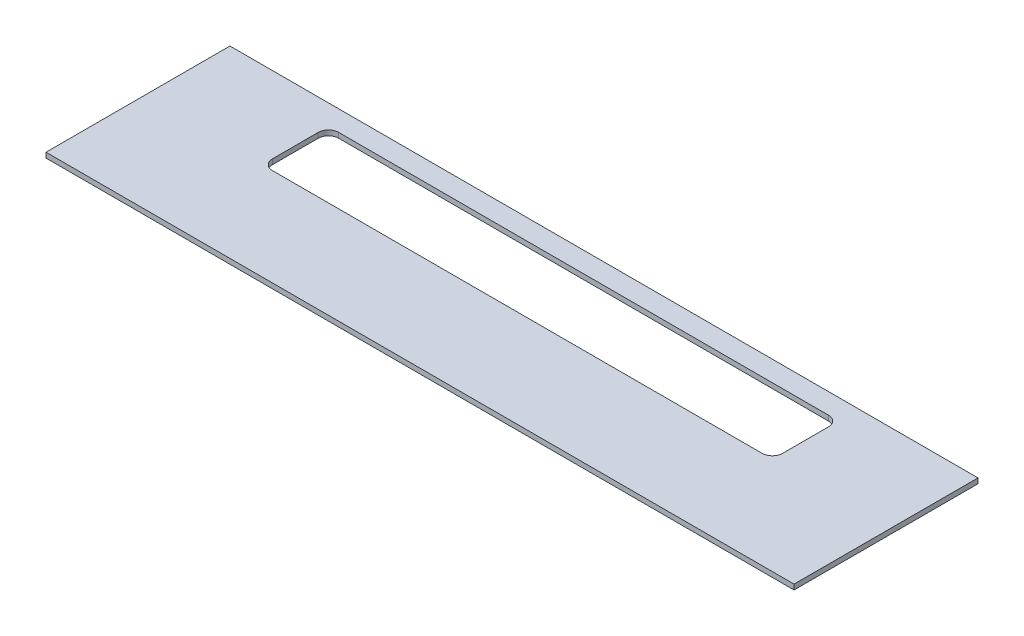
SolidWorks part; units mm, degrees
ref_plane "Front Plane" through (0, 0, 0) normal (0, 0, 1) x (1, 0, 0)
ref_plane "Top Plane" through (0, 0, 0) normal (0, 1, 0) x (1, 0, 0)
ref_plane "Right Plane" through (0, 0, 0) normal (1, 0, 0) x (0, 0, -1)
sketch "Sketch1" plane through (0, 0, 0) normal (0, 1, 0) x (1, 0, 0)
  line L1 (116.205, -28.575) -> (-116.205, -28.575)
  line L2 (116.205, -28.575) -> (116.205, 28.575)
  line L3 (116.205, 28.575) -> (-116.205, 28.575)
  line L4 (-116.205, -28.575) -> (-116.205, 28.575)
  line L5 (116.205, -28.575) -> (-116.205, 28.575) construction
  line L6 (116.205, 28.575) -> (-116.205, -28.575) construction
  point P0 (0, 0)
  dimension "D1" = 232.41
  dimension "D2" = 57.15
extrude "Boss-Extrude1" add sketch "Sketch1" along normal blind 1.5875
sketch "Sketch2" plane through (0, 1.5875, 0) normal (0, 1, 0) x (1, 0, 0)
  line L0 (-116.205, -28.575) -> (116.205, -28.575) construction
  line L1 (-79.248, 22.225) -> (79.248, 22.225)
  line L2 (-79.248, 22.225) -> (-79.248, 1.651)
  line L3 (-79.248, 1.651) -> (79.248, 1.651)
  line L4 (79.248, 22.225) -> (79.248, 1.651)
  line L5 (116.205, 28.575) -> (-116.205, 28.575) construction
  point P4 (0, 1.651)
  point P7 (0, -28.575)
  dimension "D1" = 158.496
  dimension "D2" = 20.574
  dimension "D3" = 0
  dimension "D4" = 6.35
extrude "Cut-Extrude1" cut sketch "Sketch2" against normal through all
fillet "Fillet1" radius 3.175 4 edges at (-79.248, 0.7937, -1.651) (79.248, 0.7937, -1.651) (79.248, 0.7937, -22.225) (-79.248, 0.7937, -22.225)
